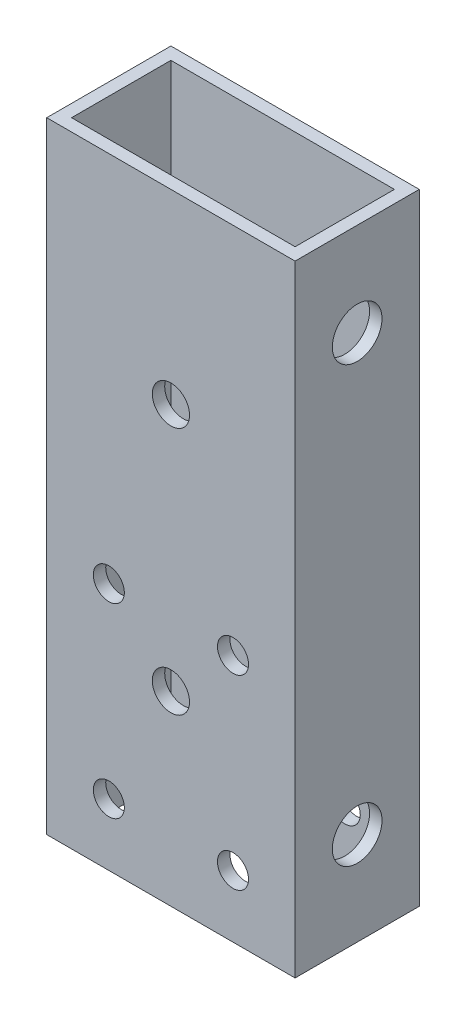
SolidWorks part; units mm, degrees
material "1060 Alloy"
ref_plane "Front" through (0, 0, 0) normal (0, 0, 1) x (1, 0, 0)
ref_plane "Top" through (0, 0, 0) normal (0, 1, 0) x (1, 0, 0)
ref_plane "Right" through (0, 0, 0) normal (1, 0, 0) x (0, 0, -1)
sketch "Skica1" plane through (0, 0, 0) normal (0, 1, 0) x (1, 0, 0)
  line L1 (0, 0) -> (40, 0)
  line L2 (0, 0) -> (0, 20)
  line L3 (0, 20) -> (40, 20)
  line L4 (40, 0) -> (40, 20)
  line L5 (2, 2) -> (38, 2)
  line L6 (2, 2) -> (2, 18)
  line L7 (2, 18) -> (38, 18)
  line L8 (38, 2) -> (38, 18)
  dimension "D1" = 40
  dimension "D2" = 20
  dimension "D3" = 2
  dimension "D4" = 2
  dimension "D5" = 36
  dimension "D6" = 16
extrude "Přidat vysunutím1" add sketch "Skica1" along normal blind 100
sketch "Skica2" plane through (40, 0, 0) normal (1, 0, 0) x (0, 0, -1)
  line L0 (0, 50) -> (50000, 50) construction
  line L2 (0, 0) -> (20, 0) construction
  line L3 (20, 100) -> (20, 0) construction
  line L4 (0, 100) -> (0, 0) construction
  circle A0 centre (10, 85) radius 4
  circle A1 centre (10, 15) radius 4
  point P8 (0, 50)
  point P11 (20, 50)
  dimension "D1" = 8
  dimension "D4" = 15
  dimension "D6" = 10
extrude "Odebrat vysunutím1" cut sketch "Skica2" against normal up to surface (40 mm away) up to face at (0, 50, -10)
sketch "Sketch1" plane through (0, 0, 0) normal (0, 0, 1) x (1, 0, 0)
  line L0 (0, 0) -> (40, 0) construction
  line L1 (0, 100) -> (0, 0) construction
  circle A0 centre (10, 10) radius 2.5
  circle A1 centre (30, 10) radius 2.5
  circle A2 centre (30, 40) radius 2.5
  circle A3 centre (10, 40) radius 2.5
  dimension "D1" = 5
  dimension "D2" = 2
  dimension "D3" = 2
  dimension "D4" = 30
  dimension "D5" = 10
  dimension "D6" = 20
  dimension "D8" = 10
extrude "Cut-Extrude1" cut sketch "Sketch1" against normal up to surface (20 mm away) up to face at (20, 50, -20)
sketch "Sketch2" plane through (0, 0, 0) normal (0, 0, 1) x (1, 0, 0)
  line L0 (0, 100) -> (0, 0) construction
  line L1 (0, 0) -> (40, 0) construction
  line L2 (0, 50) -> (50000, 50) construction
  line L3 (40, 100) -> (40, 0) construction
  circle A0 centre (20, 30) radius 3
  circle A1 centre (20, 70) radius 3
  point P8 (0, 50)
  point P11 (40, 50)
  dimension "D1" = 6
  dimension "D2" = 20
  dimension "D3" = 30
extrude "Cut-Extrude2" cut sketch "Sketch2" against normal up to surface (2 mm away) up to face at (27.5, 10, -2)
